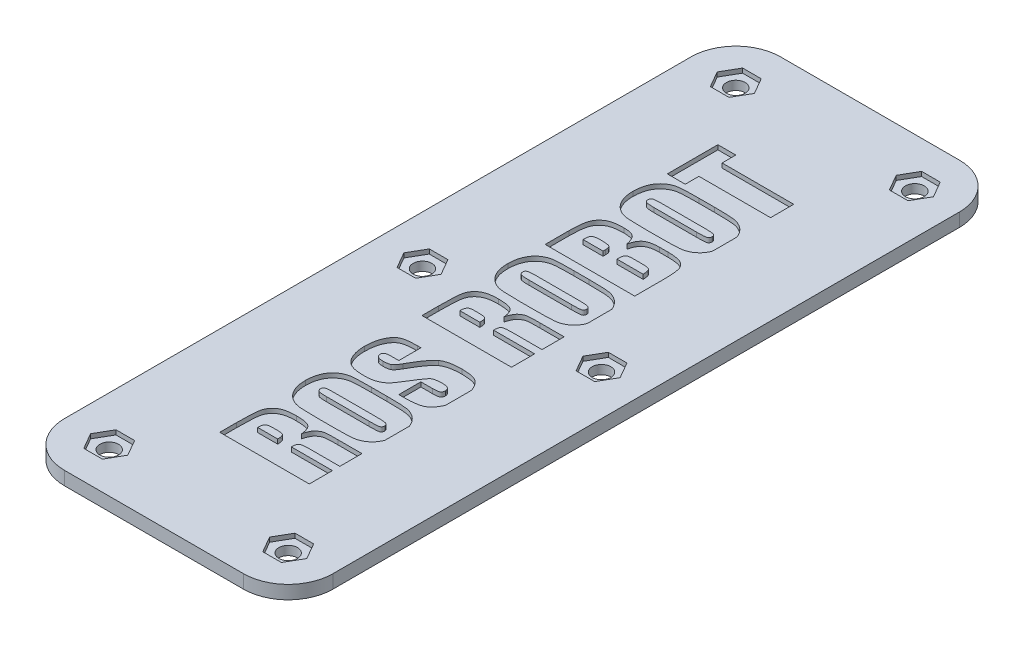
SolidWorks part; units mm, degrees
ref_plane "Front Plane" through (0, 0, 0) normal (0, 0, 1) x (1, 0, 0)
ref_plane "Top Plane" through (0, 0, 0) normal (0, 1, 0) x (1, 0, 0)
ref_plane "Right Plane" through (0, 0, 0) normal (1, 0, 0) x (0, 0, -1)
sketch "Sketch1" plane through (0, 0, 0) normal (0, 1, 0) x (1, 0, 0)
  line L1 (-30, 80) -> (30, 80)
  line L2 (-30, 80) -> (-30, -80)
  line L3 (-30, -80) -> (30, -80)
  line L4 (30, 80) -> (30, -80)
  line L5 (-30, 80) -> (30, -80) construction
  line L6 (-30, -80) -> (30, 80) construction
  point P0 (0, 0)
  dimension "D1" = 60
  dimension "D2" = 160
extrude "Boss-Extrude1" add sketch "Sketch1" along normal blind 3
sketch "Sketch2" plane through (0, 3, 0) normal (0, 1, 0) x (1, 0, 0)
  line L0 (-30, -80) -> (30, -80) construction
  line L2 (-30, 80) -> (-30, -80) construction
  circle A0 centre (-20, -70) radius 2.09
  circle A1 centre (-20, 0) radius 2.09
  circle A2 centre (-20, 70) radius 2.09
  dimension "D1" = 4.18
  dimension "D2" = 70
  dimension "D3" = 70
  dimension "D4" = 10
  dimension "D5" = 10
extrude "Cut-Extrude1" cut sketch "Sketch2" against normal through all
mirror "Mirror1" about plane through (0, 0, 0) normal (1, 0, 0) of "Cut-Extrude1"
sketch "Sketch3" plane through (0, 3, 0) normal (0, 1, 0) x (1, 0, 0)
  line L0 (10, -60) -> (10, 60)
  line L1 (-30, 80) -> (-30, -80) construction
  line L2 (-10, -55.2941) -> (-10, -51.5662)
  line L3 (4.6581, -43.5294) -> (10, -43.5294)
  line L4 (10, -43.5294) -> (10, -48.4706)
  line L5 (10, -48.4706) -> (3.2353, -48.4706)
  line L6 (0.8235, -50.1176) -> (10, -50.1176)
  line L7 (10, -50.1176) -> (10, -55.2941)
  line L8 (10, -55.2941) -> (-10, -55.2941)
  line L9 (-6.7059, -50.1176) -> (-2.2353, -50.1176)
  line L10 (-4.0478, -48.4706) -> (-5.1544, -48.4706)
  line L11 (1.7206, -41.6471) -> (-1.7206, -41.6471)
  line L12 (-1.7206, -29.6471) -> (1.7206, -29.6471)
  line L13 (-4.9596, -36.4706) -> (4.5662, -36.4706)
  line L14 (4.4154, -34.8235) -> (-4.9596, -34.8235)
  line L15 (-3.8824, -16.4706) -> (-3.8824, -21.4118)
  line L16 (-3.8824, -21.4118) -> (-5.4632, -21.4118)
  line L17 (4.0478, -28) -> (2.7059, -28)
  line L18 (2.7059, -28) -> (2.7059, -23.0588)
  line L19 (2.7059, -23.0588) -> (5.2978, -23.0588)
  line L20 (-4.6875, -16.4706) -> (-3.8824, -16.4706)
  line L21 (-10, -10.1176) -> (-10, -6.3897)
  line L22 (4.6581, 1.6471) -> (10, 1.6471)
  line L23 (10, 1.6471) -> (10, -3.2941)
  line L24 (10, -3.2941) -> (3.2353, -3.2941)
  line L25 (0.8235, -4.9412) -> (10, -4.9412)
  line L26 (10, -4.9412) -> (10, -10.1176)
  line L27 (10, -10.1176) -> (-10, -10.1176)
  line L28 (-6.7059, -4.9412) -> (-2.2353, -4.9412)
  line L29 (-4.0478, -3.2941) -> (-5.1544, -3.2941)
  line L30 (1.7206, 3.5294) -> (-1.7206, 3.5294)
  line L31 (-1.7206, 15.5294) -> (1.7206, 15.5294)
  line L32 (-4.9596, 8.7059) -> (4.5662, 8.7059)
  line L33 (4.4154, 10.3529) -> (-4.9596, 10.3529)
  line L34 (-10, 17.4118) -> (-10, 22.7169)
  line L35 (3.364, 29.6471) -> (5.2426, 29.6471)
  line L36 (10, 23.4926) -> (10, 17.4118)
  line L37 (10, 17.4118) -> (-10, 17.4118)
  line L38 (-6.7059, 22.5882) -> (-2.2353, 22.5882)
  line L39 (0.8235, 22.5882) -> (6.7059, 22.5882)
  line L40 (4.7463, 24.4706) -> (2.7831, 24.4706)
  line L41 (1.7206, 31.5294) -> (-1.7206, 31.5294)
  line L42 (-1.7206, 43.5294) -> (1.7206, 43.5294)
  line L43 (-4.9596, 36.7059) -> (4.5662, 36.7059)
  line L44 (4.4154, 38.3529) -> (-4.9596, 38.3529)
  line L45 (-10, 56) -> (-6, 56)
  line L46 (-6, 56) -> (-6, 52.9412)
  line L47 (-6, 52.9412) -> (10, 52.9412)
  line L48 (10, 52.9412) -> (10, 47.7647)
  line L49 (10, 47.7647) -> (-6, 47.7647)
  line L50 (-6, 47.7647) -> (-6, 44.7059)
  line L51 (-6, 44.7059) -> (-10, 44.7059)
  line L52 (-10, 44.7059) -> (-10, 56)
  spline S0 degree 3 poles (-10, -51.5662) (-10.0021, -50.9938) (-9.9925, -50.1738) (-9.9618, -49.131) (-9.9343, -48.4616) (-9.8938, -47.8671) (-9.8469, -47.3485) (-9.7938, -46.9053) (-9.7279, -46.5265) (-9.6422, -46.1927) (-9.5296, -45.8846) (-9.3956, -45.5898) (-9.2282, -45.3117) (-9.0316, -45.0523) (-8.8156, -44.8023) (-8.5646, -44.5748) (-8.2904, -44.3559) (-7.9777, -44.158) (-7.6226, -43.9907) (-7.2263, -43.847) (-6.7869, -43.7305) (-6.3051, -43.6403) (-5.579, -43.5478) (-5.0099, -43.5348) (-4.6176, -43.5294) knots 0 0 0 0 0.148881 0.213303 0.271377 0.323138 0.368276 0.406827 0.439217 0.468212 0.496346 0.524443 0.552325 0.580569 0.609028 0.638128 0.668547 0.700209 0.734143 0.770448 0.80973 0.852244 0.897872 1 1 1 1
  spline S1 degree 3 poles (-4.6176, -43.5294) (-4.2653, -43.5236) (-3.7599, -43.5474) (-3.1182, -43.6025) (-2.7075, -43.671) (-2.3432, -43.7491) (-2.0238, -43.8459) (-1.7543, -43.9676) (-1.5246, -44.1057) (-1.3304, -44.2743) (-1.1605, -44.4757) (-1.0104, -44.7121) (-0.8806, -44.9835) (-0.7776, -45.291) (-0.6464, -45.7633) (-0.5975, -46.1443) (-0.5735, -46.4081) knots 0 0 0 0 0.183844 0.264214 0.336185 0.401092 0.458783 0.510057 0.555172 0.598283 0.643683 0.692329 0.744143 0.800414 0.861431 1 1 1 1
  spline S2 degree 3 poles (-0.5735, -46.4081) (-0.5082, -46.1692) (-0.4158, -45.8227) (-0.2536, -45.3924) (-0.1242, -45.1174) (0.0082, -44.8722) (0.1462, -44.6567) (0.2982, -44.4752) (0.5056, -44.2791) (0.7695, -44.0853) (1.0739, -43.8901) (1.3668, -43.7472) (1.6163, -43.6653) (1.8438, -43.6284) (2.0703, -43.5981) (2.3577, -43.579) (2.7033, -43.5604) (3.1078, -43.5466) (3.7658, -43.5296) (4.2893, -43.5348) (4.6581, -43.5294) knots 0 0 0 0 0.11021 0.159198 0.204304 0.245276 0.283065 0.317885 0.350264 0.409778 0.463156 0.510931 0.554366 0.579275 0.613344 0.655979 0.70728 0.767268 0.835956 1 1 1 1
  spline S3 degree 3 poles (3.2353, -48.4706) (2.989, -48.4726) (2.6391, -48.4726) (2.1993, -48.5048) (1.9269, -48.5332) (1.6924, -48.5693) (1.4957, -48.6105) (1.339, -48.6657) (1.2146, -48.7289) (1.114, -48.8112) (1.0393, -48.9233) (0.9667, -49.0542) (0.9194, -49.2179) (0.8733, -49.4037) (0.8356, -49.7073) (0.824, -49.9481) (0.8235, -50.1176) knots 0 0 0 0 0.208735 0.296167 0.373443 0.440695 0.497113 0.543415 0.581035 0.614932 0.652106 0.694368 0.741317 0.795712 0.856499 1 1 1 1
  spline S4 degree 3 poles (-2.2353, -50.1176) (-2.241, -49.859) (-2.2449, -49.4942) (-2.3595, -49.0703) (-2.4455, -48.8674) (-2.5571, -48.7457) (-2.6702, -48.6674) (-2.8204, -48.6082) (-3.0015, -48.5571) (-3.2158, -48.5182) (-3.5672, -48.4758) (-3.8494, -48.4762) (-4.0478, -48.4706) knots 0 0 0 0 0.26299 0.361623 0.442867 0.481356 0.526611 0.580322 0.643299 0.716254 0.799641 1 1 1 1
  spline S5 degree 3 poles (-5.1544, -48.4706) (-5.4183, -48.4732) (-5.7882, -48.4915) (-6.209, -48.649) (-6.422, -48.8134) (-6.5523, -49.0502) (-6.6913, -49.4796) (-6.7008, -49.8538) (-6.7059, -50.1176) knots 0 0 0 0 0.296724 0.405999 0.497474 0.590179 0.702697 1 1 1 1
  spline S6 degree 3 poles (1.7206, -29.6471) (2.1887, -29.6516) (2.8628, -29.6489) (3.7244, -29.6629) (4.2868, -29.6838) (4.7956, -29.6992) (5.249, -29.7256) (5.6474, -29.7548) (6.1016, -29.7961) (6.625, -29.8819) (7.2194, -30.0688) (7.7848, -30.3319) (8.3184, -30.6676) (8.8126, -31.0692) (9.2459, -31.5466) (9.6203, -32.0876) (9.9272, -32.6949) (10.1748, -33.3563) (10.4086, -34.3407) (10.4749, -35.116) (10.4706, -35.6471) knots 0 0 0 0 0.113101 0.162848 0.208171 0.249056 0.285827 0.31789 0.345554 0.396029 0.44566 0.495598 0.546282 0.597611 0.648955 0.701516 0.75607 0.812935 0.871747 1 1 1 1
  spline S7 degree 3 poles (10.4706, -35.6471) (10.4702, -36.1567) (10.4117, -36.9073) (10.1869, -37.8648) (9.9551, -38.5228) (9.666, -39.1346) (9.2939, -39.6787) (8.8684, -40.1717) (8.3693, -40.5862) (7.8326, -40.9353) (7.2648, -41.2061) (6.6744, -41.4) (6.1562, -41.4954) (5.705, -41.5355) (5.3079, -41.5652) (4.8519, -41.59) (4.3384, -41.6129) (3.766, -41.6259) (2.8873, -41.6415) (2.1985, -41.6458) (1.7206, -41.6471) knots 0 0 0 0 0.123187 0.181008 0.237203 0.291505 0.343988 0.396026 0.44835 0.500181 0.550382 0.599921 0.649928 0.677302 0.709372 0.746151 0.787647 0.833563 0.884505 1 1 1 1
  spline S8 degree 3 poles (-1.7206, -41.6471) (-2.1875, -41.6426) (-2.8616, -41.6453) (-3.7232, -41.6312) (-4.2868, -41.6107) (-4.7942, -41.5935) (-5.2479, -41.5731) (-5.6461, -41.5428) (-6.102, -41.5024) (-6.6245, -41.4108) (-7.2196, -41.2259) (-7.7852, -40.961) (-8.3211, -40.6288) (-8.8141, -40.2235) (-9.2437, -39.7445) (-9.6213, -39.2061) (-9.9283, -38.5999) (-10.1693, -37.9353) (-10.4131, -36.9536) (-10.4652, -36.1757) (-10.4706, -35.6471) knots 0 0 0 0 0.112808 0.162853 0.208178 0.249064 0.285525 0.317884 0.345549 0.396077 0.445709 0.495649 0.546586 0.597688 0.649252 0.701572 0.756128 0.812892 0.872063 1 1 1 1
  spline S9 degree 3 poles (-10.4706, -35.6471) (-10.4714, -35.1372) (-10.4096, -34.3888) (-10.1907, -33.4315) (-9.9597, -32.7739) (-9.664, -32.1639) (-9.2966, -31.6157) (-8.8667, -31.1263) (-8.3697, -30.7111) (-7.8316, -30.3634) (-7.2658, -30.087) (-6.6754, -29.8952) (-6.1588, -29.7978) (-5.7072, -29.7597) (-5.3094, -29.7227) (-4.8517, -29.7062) (-4.3385, -29.6803) (-3.7659, -29.6698) (-2.8875, -29.6434) (-2.1984, -29.6546) (-1.7206, -29.6471) knots 0 0 0 0 0.123194 0.180663 0.236861 0.291296 0.344027 0.395847 0.448174 0.500008 0.55034 0.599882 0.649601 0.676977 0.709367 0.746132 0.787631 0.833549 0.884501 1 1 1 1
  spline S10 degree 3 poles (-4.9596, -34.8235) (-5.1753, -34.8242) (-5.4829, -34.83) (-5.8716, -34.843) (-6.1155, -34.8622) (-6.3276, -34.8839) (-6.5086, -34.9074) (-6.6559, -34.9406) (-6.806, -34.9862) (-6.954, -35.0702) (-7.1431, -35.2687) (-7.1725, -35.486) (-7.1765, -35.6213) knots 0 0 0 0 0.245382 0.350014 0.44228 0.523563 0.592561 0.649714 0.69512 0.770679 0.840726 1 1 1 1
  spline S11 degree 3 poles (-7.1765, -35.6213) (-7.1826, -35.7474) (-7.1389, -35.933) (-7.0007, -36.1393) (-6.8803, -36.2454) (-6.7481, -36.3134) (-6.606, -36.3546) (-6.4264, -36.3903) (-6.2075, -36.4176) (-5.9516, -36.4453) (-5.5307, -36.4612) (-5.1963, -36.473) (-4.9596, -36.4706) knots 0 0 0 0 0.14123 0.20787 0.277368 0.319365 0.374393 0.44345 0.525667 0.62281 0.733417 1 1 1 1
  spline S12 degree 3 poles (4.5662, -36.4706) (4.8346, -36.4661) (5.2158, -36.4689) (5.6951, -36.4552) (5.9902, -36.4341) (6.2432, -36.4194) (6.4541, -36.3928) (6.6225, -36.365) (6.7864, -36.3252) (6.9456, -36.2427) (7.1431, -36.032) (7.1757, -35.8027) (7.1765, -35.6581) knots 0 0 0 0 0.263966 0.37491 0.47152 0.554902 0.624119 0.680394 0.722784 0.789642 0.853612 1 1 1 1
  spline S13 degree 3 poles (7.1765, -35.6581) (7.1748, -35.5096) (7.1356, -35.267) (6.9074, -35.0588) (6.7277, -34.9785) (6.5458, -34.9318) (6.3632, -34.9057) (6.1401, -34.8796) (5.8753, -34.8573) (5.5687, -34.8447) (5.0773, -34.8286) (4.6887, -34.825) (4.4154, -34.8235) knots 0 0 0 0 0.144509 0.209626 0.282207 0.327425 0.385695 0.455209 0.538352 0.635125 0.743353 1 1 1 1
  spline S14 degree 3 poles (-5.4632, -21.4118) (-5.765, -21.4118) (-6.1723, -21.4209) (-6.6458, -21.5046) (-6.8672, -21.593) (-7.0158, -21.7183) (-7.1437, -21.9403) (-7.1819, -22.1356) (-7.1765, -22.2721) knots 0 0 0 0 0.412531 0.554325 0.654756 0.734266 0.814634 1 1 1 1
  spline S15 degree 3 poles (-7.1765, -22.2721) (-7.1753, -22.4224) (-7.1339, -22.6526) (-6.9564, -22.8986) (-6.7779, -23.0494) (-6.5473, -23.1638) (-6.1427, -23.267) (-5.8109, -23.3007) (-5.5735, -23.2941) knots 0 0 0 0 0.212113 0.312859 0.418563 0.535756 0.66915 1 1 1 1
  spline S16 degree 3 poles (-5.5735, -23.2941) (-5.2685, -23.2963) (-4.7355, -23.2666) (-4.2139, -23.1434) (-4.0074, -23.0441) knots 0 0 0 0 0.572651 1 1 1 1
  spline S17 degree 3 poles (-4.0074, -23.0441) (-3.9087, -22.9953) (-3.7635, -22.892) (-3.5783, -22.7165) (-3.4317, -22.5391) (-3.2741, -22.3344) (-3.0492, -21.9996) (-2.8928, -21.7223) (-2.7831, -21.5294) knots 0 0 0 0 0.166753 0.269572 0.387216 0.516182 0.662459 1 1 1 1
  spline S18 degree 3 poles (-2.7831, -21.5294) (-2.4734, -20.9703) (-2.0184, -20.1729) (-1.3881, -19.1897) (-0.9563, -18.5738) (-0.5522, -18.0389) (-0.0677, -17.4805) (0.3024, -17.1194) (0.5662, -16.9375) knots 0 0 0 0 0.335278 0.4813 0.612364 0.729739 0.832713 1 1 1 1
  spline S19 degree 3 poles (0.5662, -16.9375) (0.806, -16.77) (1.2115, -16.5589) (1.8106, -16.3573) (2.3243, -16.226) (2.8906, -16.1237) (3.7446, -16.0244) (4.4137, -16) (4.875, -16) knots 0 0 0 0 0.195997 0.304678 0.423526 0.551406 0.690506 1 1 1 1
  spline S20 degree 3 poles (4.875, -16) (5.2122, -15.9983) (5.6998, -16.0135) (6.3256, -16.0701) (6.7422, -16.1221) (7.1236, -16.1969) (7.469, -16.2838) (7.7801, -16.385) (8.0583, -16.5087) (8.3139, -16.656) (8.557, -16.8277) (8.7858, -17.0338) (9.0067, -17.2654) (9.2179, -17.528) (9.4131, -17.8237) (9.6079, -18.1433) (9.8414, -18.6198) (10.1006, -19.2594) (10.3969, -20.3943) (10.4676, -21.2925) (10.4706, -21.9044) knots 0 0 0 0 0.107325 0.155097 0.199939 0.240858 0.278693 0.313224 0.344823 0.375395 0.406993 0.439316 0.473245 0.508753 0.546395 0.585923 0.627781 0.715119 0.805079 1 1 1 1
  spline S21 degree 3 poles (10.4706, -21.9044) (10.4757, -22.2484) (10.4446, -22.7548) (10.3628, -23.4141) (10.2732, -23.8804) (10.1612, -24.328) (10.0192, -24.7555) (9.8605, -25.1658) (9.6676, -25.5494) (9.4591, -25.9093) (9.2368, -26.2396) (8.9991, -26.5368) (8.7496, -26.8027) (8.4841, -27.0361) (8.2022, -27.235) (7.9096, -27.4062) (7.5968, -27.5388) (7.2633, -27.6501) (6.9011, -27.7452) (6.505, -27.82) (6.0773, -27.8875) (5.616, -27.9373) (4.936, -27.9878) (4.4094, -27.9998) (4.0478, -28) knots 0 0 0 0 0.100148 0.147671 0.19347 0.238417 0.282003 0.324638 0.366476 0.406958 0.44578 0.482362 0.517724 0.551885 0.585175 0.618127 0.650431 0.683967 0.720516 0.759451 0.801367 0.846634 0.894615 1 1 1 1
  spline S22 degree 3 poles (5.2978, -23.0588) (5.4794, -23.0613) (5.7378, -23.049) (6.0657, -23.0335) (6.2711, -23.0047) (6.4517, -22.98) (6.6031, -22.9371) (6.7301, -22.8953) (6.8628, -22.8277) (6.9937, -22.7117) (7.1506, -22.4544) (7.1729, -22.2151) (7.1765, -22.0551) knots 0 0 0 0 0.221449 0.31586 0.400263 0.474516 0.538003 0.591926 0.637412 0.719013 0.801608 1 1 1 1
  spline S23 degree 3 poles (7.1765, -22.0551) (7.1797, -21.8865) (7.1319, -21.6346) (6.944, -21.3618) (6.7516, -21.2047) (6.511, -21.0827) (6.094, -20.9668) (5.75, -20.942) (5.5074, -20.9412) knots 0 0 0 0 0.223439 0.325747 0.431377 0.547858 0.679404 1 1 1 1
  spline S24 degree 3 poles (5.5074, -20.9412) (5.2301, -20.9407) (4.8335, -20.9536) (4.3315, -21.0008) (4.0144, -21.0585) (3.7334, -21.12) (3.4321, -21.228) (3.2311, -21.3302) (3.125, -21.4228) knots 0 0 0 0 0.33668 0.481833 0.611779 0.728037 0.830669 1 1 1 1
  spline S25 degree 3 poles (3.125, -21.4228) (3.0067, -21.5278) (2.832, -21.7237) (2.5986, -22.0274) (2.3862, -22.3232) (2.1458, -22.6637) (1.7857, -23.219) (1.5142, -23.6656) (1.3235, -23.9779) knots 0 0 0 0 0.151179 0.250673 0.366592 0.499698 0.649697 1 1 1 1
  spline S26 degree 3 poles (1.3235, -23.9779) (1.1312, -24.2944) (0.8539, -24.7471) (0.4867, -25.3154) (0.2465, -25.6779) (0.024, -25.9952) (-0.1732, -26.2708) (-0.3489, -26.5042) (-0.5602, -26.7562) (-0.8385, -27.0321) (-1.2198, -27.322) (-1.6571, -27.5826) (-2.1499, -27.8167) (-2.7079, -28.0109) (-3.5918, -28.187) (-4.2954, -28.2419) (-4.7868, -28.2353) knots 0 0 0 0 0.139506 0.199942 0.254867 0.303273 0.345934 0.382495 0.413289 0.469759 0.52968 0.593251 0.661185 0.734906 0.815121 1 1 1 1
  spline S27 degree 3 poles (-4.7868, -28.2353) (-5.1483, -28.2299) (-5.6721, -28.2229) (-6.342, -28.1555) (-6.7866, -28.0911) (-7.1929, -28.0062) (-7.5618, -27.9063) (-7.8893, -27.7803) (-8.183, -27.6392) (-8.4486, -27.4744) (-8.6932, -27.2854) (-8.9296, -27.0793) (-9.1431, -26.8428) (-9.3479, -26.5869) (-9.5388, -26.3089) (-9.711, -26.0053) (-9.9259, -25.5665) (-10.1466, -24.9651) (-10.4114, -23.8851) (-10.4702, -23.0241) (-10.4706, -22.4338) knots 0 0 0 0 0.115094 0.16642 0.214115 0.25793 0.298418 0.335563 0.369391 0.401957 0.434786 0.46765 0.501588 0.535991 0.571894 0.608743 0.64693 0.727243 0.81197 1 1 1 1
  spline S28 degree 3 poles (-10.4706, -22.4338) (-10.4681, -22.0991) (-10.4534, -21.6059) (-10.3832, -20.9641) (-10.3105, -20.511) (-10.2136, -20.0772) (-10.102, -19.6612) (-9.9641, -19.2668) (-9.8111, -18.8916) (-9.6395, -18.5421) (-9.457, -18.2203) (-9.2585, -17.9336) (-9.0613, -17.6686) (-8.8392, -17.446) (-8.617, -17.2428) (-8.377, -17.0786) (-8.1223, -16.9405) (-7.8384, -16.8309) (-7.5198, -16.7307) (-7.1549, -16.6529) (-6.7482, -16.5815) (-6.2949, -16.5328) (-5.6039, -16.4819) (-5.0626, -16.471) (-4.6875, -16.4706) knots 0 0 0 0 0.103075 0.151642 0.198646 0.244222 0.288419 0.331123 0.37273 0.413047 0.450895 0.486465 0.520341 0.552351 0.583079 0.612899 0.641587 0.672056 0.706415 0.744299 0.786776 0.83347 0.88453 1 1 1 1
  spline S29 degree 3 poles (-10, -6.3897) (-10.0021, -5.8173) (-9.9925, -4.9973) (-9.9618, -3.9545) (-9.9343, -3.2851) (-9.8938, -2.6907) (-9.8469, -2.172) (-9.7938, -1.7288) (-9.7279, -1.3501) (-9.6422, -1.0162) (-9.5296, -0.7081) (-9.3956, -0.4133) (-9.2282, -0.1353) (-9.0316, 0.1241) (-8.8156, 0.3741) (-8.5646, 0.6016) (-8.2904, 0.8205) (-7.9777, 1.0184) (-7.6226, 1.1858) (-7.2263, 1.3294) (-6.7869, 1.4459) (-6.3051, 1.5362) (-5.579, 1.6287) (-5.0099, 1.6416) (-4.6176, 1.6471) knots 0 0 0 0 0.148881 0.213303 0.271377 0.323138 0.368276 0.406827 0.439217 0.468212 0.496346 0.524443 0.552325 0.580569 0.609028 0.638128 0.668547 0.700209 0.734143 0.770448 0.80973 0.852244 0.897872 1 1 1 1
  spline S30 degree 3 poles (-4.6176, 1.6471) (-4.2653, 1.6529) (-3.7599, 1.629) (-3.1182, 1.574) (-2.7075, 1.5055) (-2.3432, 1.4273) (-2.0238, 1.3305) (-1.7543, 1.2089) (-1.5246, 1.0707) (-1.3304, 0.9022) (-1.1605, 0.7008) (-1.0104, 0.4644) (-0.8806, 0.1929) (-0.7776, -0.1145) (-0.6464, -0.5869) (-0.5975, -0.9678) (-0.5735, -1.2316) knots 0 0 0 0 0.183844 0.264214 0.336185 0.401092 0.458783 0.510057 0.555172 0.598283 0.643683 0.692329 0.744143 0.800414 0.861431 1 1 1 1
  spline S31 degree 3 poles (-0.5735, -1.2316) (-0.5082, -0.9927) (-0.4158, -0.6463) (-0.2536, -0.216) (-0.1242, 0.0591) (0.0082, 0.3043) (0.1462, 0.5197) (0.2982, 0.7013) (0.5056, 0.8974) (0.7695, 1.0911) (1.0739, 1.2863) (1.3668, 1.4293) (1.6163, 1.5112) (1.8438, 1.5481) (2.0703, 1.5783) (2.3577, 1.5974) (2.7033, 1.6161) (3.1078, 1.6299) (3.7658, 1.6469) (4.2893, 1.6416) (4.6581, 1.6471) knots 0 0 0 0 0.11021 0.159198 0.204304 0.245276 0.283065 0.317885 0.350264 0.409778 0.463156 0.510931 0.554366 0.579275 0.613344 0.655979 0.70728 0.767268 0.835956 1 1 1 1
  spline S32 degree 3 poles (3.2353, -3.2941) (2.989, -3.2962) (2.6391, -3.2961) (2.1993, -3.3283) (1.9269, -3.3567) (1.6924, -3.3928) (1.4957, -3.4341) (1.339, -3.4893) (1.2146, -3.5525) (1.114, -3.6348) (1.0393, -3.7469) (0.9667, -3.8778) (0.9194, -4.0414) (0.8733, -4.2272) (0.8356, -4.5308) (0.824, -4.7717) (0.8235, -4.9412) knots 0 0 0 0 0.208735 0.296167 0.373443 0.440695 0.497113 0.543415 0.581035 0.614932 0.652106 0.694368 0.741317 0.795712 0.856499 1 1 1 1
  spline S33 degree 3 poles (-2.2353, -4.9412) (-2.241, -4.6826) (-2.2449, -4.3177) (-2.3595, -3.8938) (-2.4455, -3.6909) (-2.5571, -3.5692) (-2.6702, -3.491) (-2.8204, -3.4317) (-3.0015, -3.3807) (-3.2158, -3.3417) (-3.5672, -3.2993) (-3.8494, -3.2997) (-4.0478, -3.2941) knots 0 0 0 0 0.26299 0.361623 0.442867 0.481356 0.526611 0.580322 0.643299 0.716254 0.799641 1 1 1 1
  spline S34 degree 3 poles (-5.1544, -3.2941) (-5.4183, -3.2968) (-5.7882, -3.315) (-6.209, -3.4725) (-6.422, -3.6369) (-6.5523, -3.8737) (-6.6913, -4.3032) (-6.7008, -4.6773) (-6.7059, -4.9412) knots 0 0 0 0 0.296724 0.405999 0.497474 0.590179 0.702697 1 1 1 1
  spline S35 degree 3 poles (1.7206, 15.5294) (2.1887, 15.5249) (2.8628, 15.5276) (3.7244, 15.5136) (4.2868, 15.4926) (4.7956, 15.4773) (5.249, 15.4509) (5.6474, 15.4217) (6.1016, 15.3804) (6.625, 15.2946) (7.2194, 15.1077) (7.7848, 14.8446) (8.3184, 14.5089) (8.8126, 14.1073) (9.2459, 13.6298) (9.6203, 13.0889) (9.9272, 12.4816) (10.1748, 11.8202) (10.4086, 10.8357) (10.4749, 10.0605) (10.4706, 9.5294) knots 0 0 0 0 0.113101 0.162848 0.208171 0.249056 0.285827 0.31789 0.345554 0.396029 0.44566 0.495598 0.546282 0.597611 0.648955 0.701516 0.75607 0.812935 0.871747 1 1 1 1
  spline S36 degree 3 poles (10.4706, 9.5294) (10.4702, 9.0198) (10.4117, 8.2692) (10.1869, 7.3116) (9.9551, 6.6537) (9.666, 6.0419) (9.2939, 5.4977) (8.8684, 5.0048) (8.3693, 4.5903) (7.8326, 4.2412) (7.2648, 3.9704) (6.6744, 3.7764) (6.1562, 3.681) (5.705, 3.6409) (5.3079, 3.6113) (4.8519, 3.5865) (4.3384, 3.5636) (3.766, 3.5505) (2.8873, 3.535) (2.1985, 3.5307) (1.7206, 3.5294) knots 0 0 0 0 0.123187 0.181008 0.237203 0.291505 0.343988 0.396026 0.44835 0.500181 0.550382 0.599921 0.649928 0.677302 0.709372 0.746151 0.787647 0.833563 0.884505 1 1 1 1
  spline S37 degree 3 poles (-1.7206, 3.5294) (-2.1875, 3.5339) (-2.8616, 3.5312) (-3.7232, 3.5453) (-4.2868, 3.5657) (-4.7942, 3.5829) (-5.2479, 3.6034) (-5.6461, 3.6337) (-6.102, 3.674) (-6.6245, 3.7656) (-7.2196, 3.9505) (-7.7852, 4.2155) (-8.3211, 4.5477) (-8.8141, 4.953) (-9.2437, 5.432) (-9.6213, 5.9703) (-9.9283, 6.5765) (-10.1693, 7.2411) (-10.4131, 8.2229) (-10.4652, 9.0008) (-10.4706, 9.5294) knots 0 0 0 0 0.112808 0.162853 0.208178 0.249064 0.285525 0.317884 0.345549 0.396077 0.445709 0.495649 0.546586 0.597688 0.649252 0.701572 0.756128 0.812892 0.872063 1 1 1 1
  spline S38 degree 3 poles (-10.4706, 9.5294) (-10.4714, 10.0393) (-10.4096, 10.7877) (-10.1907, 11.7449) (-9.9597, 12.4026) (-9.664, 13.0126) (-9.2966, 13.5607) (-8.8667, 14.0501) (-8.3697, 14.4654) (-7.8316, 14.813) (-7.2658, 15.0895) (-6.6754, 15.2813) (-6.1588, 15.3787) (-5.7072, 15.4167) (-5.3094, 15.4538) (-4.8517, 15.4703) (-4.3385, 15.4962) (-3.7659, 15.5067) (-2.8875, 15.5331) (-2.1984, 15.5218) (-1.7206, 15.5294) knots 0 0 0 0 0.123194 0.180663 0.236861 0.291296 0.344027 0.395847 0.448174 0.500008 0.55034 0.599882 0.649601 0.676977 0.709367 0.746132 0.787631 0.833549 0.884501 1 1 1 1
  spline S39 degree 3 poles (-4.9596, 10.3529) (-5.1753, 10.3523) (-5.4829, 10.3464) (-5.8716, 10.3334) (-6.1155, 10.3143) (-6.3276, 10.2926) (-6.5086, 10.2691) (-6.6559, 10.2359) (-6.806, 10.1902) (-6.954, 10.1063) (-7.1431, 9.9078) (-7.1725, 9.6905) (-7.1765, 9.5551) knots 0 0 0 0 0.245382 0.350014 0.44228 0.523563 0.592561 0.649714 0.69512 0.770679 0.840726 1 1 1 1
  spline S40 degree 3 poles (-7.1765, 9.5551) (-7.1826, 9.4291) (-7.1389, 9.2435) (-7.0007, 9.0372) (-6.8803, 8.931) (-6.7481, 8.8631) (-6.606, 8.8219) (-6.4264, 8.7862) (-6.2075, 8.7588) (-5.9516, 8.7312) (-5.5307, 8.7153) (-5.1963, 8.7035) (-4.9596, 8.7059) knots 0 0 0 0 0.14123 0.20787 0.277368 0.319365 0.374393 0.44345 0.525667 0.62281 0.733417 1 1 1 1
  spline S41 degree 3 poles (4.5662, 8.7059) (4.8346, 8.7104) (5.2158, 8.7076) (5.6951, 8.7213) (5.9902, 8.7424) (6.2432, 8.7571) (6.4541, 8.7836) (6.6225, 8.8115) (6.7864, 8.8513) (6.9456, 8.9338) (7.1431, 9.1444) (7.1757, 9.3737) (7.1765, 9.5184) knots 0 0 0 0 0.263966 0.37491 0.47152 0.554902 0.624119 0.680394 0.722784 0.789642 0.853612 1 1 1 1
  spline S42 degree 3 poles (7.1765, 9.5184) (7.1748, 9.6669) (7.1356, 9.9095) (6.9074, 10.1176) (6.7277, 10.198) (6.5458, 10.2447) (6.3632, 10.2708) (6.1401, 10.2969) (5.8753, 10.3191) (5.5687, 10.3318) (5.0773, 10.3479) (4.6887, 10.3515) (4.4154, 10.3529) knots 0 0 0 0 0.144509 0.209626 0.282207 0.327425 0.385695 0.455209 0.538352 0.635125 0.743353 1 1 1 1
  spline S43 degree 3 poles (-10, 22.7169) (-9.9955, 23.1103) (-9.9921, 23.6819) (-9.9527, 24.4186) (-9.9071, 24.9135) (-9.857, 25.3711) (-9.7961, 25.7911) (-9.7188, 26.1725) (-9.6309, 26.5207) (-9.5237, 26.8424) (-9.3912, 27.1434) (-9.2355, 27.4283) (-9.0587, 27.6987) (-8.8552, 27.9531) (-8.6276, 28.1917) (-8.375, 28.4137) (-8.0977, 28.6217) (-7.7862, 28.8126) (-7.4301, 28.9734) (-7.0293, 29.1081) (-6.5873, 29.2218) (-6.1, 29.3043) (-5.3665, 29.3894) (-4.791, 29.4161) (-4.3934, 29.4118) knots 0 0 0 0 0.114375 0.166108 0.21439 0.258844 0.299904 0.337701 0.371916 0.404248 0.43615 0.467396 0.498519 0.529953 0.561953 0.594259 0.627603 0.66261 0.70023 0.740899 0.785396 0.832777 0.884431 1 1 1 1
  spline S44 degree 3 poles (-4.3934, 29.4118) (-4.127, 29.416) (-3.7431, 29.3962) (-3.2561, 29.335) (-2.9376, 29.2799) (-2.6536, 29.1963) (-2.3989, 29.1046) (-2.1784, 28.9884) (-1.985, 28.8544) (-1.8163, 28.6891) (-1.6558, 28.4982) (-1.5162, 28.2669) (-1.3783, 28.0074) (-1.2489, 27.7134) (-1.0963, 27.2527) (-0.9938, 26.8887) (-0.9412, 26.6324) knots 0 0 0 0 0.159635 0.229972 0.294227 0.35305 0.407212 0.456169 0.502024 0.547743 0.597307 0.65111 0.709269 0.77341 0.843331 1 1 1 1
  spline S45 degree 3 poles (-0.9412, 26.6324) (-0.8783, 26.9064) (-0.7658, 27.3007) (-0.5629, 27.7876) (-0.4027, 28.1069) (-0.2205, 28.3873) (-0.0268, 28.6367) (0.1878, 28.8487) (0.4252, 29.025) (0.6872, 29.1721) (0.9755, 29.3025) (1.2968, 29.4066) (1.6481, 29.495) (2.0311, 29.565) (2.6061, 29.6282) (3.0548, 29.6461) (3.364, 29.6471) knots 0 0 0 0 0.144043 0.209309 0.269932 0.32668 0.380292 0.431325 0.480651 0.531247 0.584899 0.64245 0.703941 0.770287 0.841669 1 1 1 1
  spline S46 degree 3 poles (5.2426, 29.6471) (5.5626, 29.6468) (6.0268, 29.6352) (6.6234, 29.5846) (7.0212, 29.535) (7.3857, 29.4682) (7.7163, 29.3886) (8.0154, 29.2938) (8.3632, 29.1496) (8.7467, 28.9274) (9.131, 28.5817) (9.4335, 28.1642) (9.6212, 27.7575) (9.7292, 27.3755) (9.8021, 27.0179) (9.8619, 26.5942) (9.9131, 26.1025) (9.9518, 25.5458) (9.9944, 24.6684) (9.9944, 23.9766) (10, 23.4926) knots 0 0 0 0 0.102269 0.148253 0.191288 0.230306 0.266588 0.299901 0.330446 0.386794 0.440584 0.494395 0.550463 0.582684 0.621084 0.666995 0.719365 0.779044 0.845298 1 1 1 1
  spline S47 degree 2 poles (-2.2353, 22.5882) (-2.243, 22.875) (-2.2463, 23.1618) knots 0 0 0 1 1 1
  spline S48 degree 3 poles (-2.2463, 23.1618) (-2.2431, 23.394) (-2.2711, 23.7204) (-2.4403, 24.0836) (-2.5925, 24.231) (-2.7527, 24.3011) (-2.9141, 24.3494) (-3.1208, 24.3814) (-3.3706, 24.4159) (-3.6639, 24.4398) (-4.143, 24.4659) (-4.5245, 24.4702) (-4.7941, 24.4706) knots 0 0 0 0 0.207117 0.283923 0.350831 0.389245 0.438074 0.499907 0.574465 0.661754 0.760817 1 1 1 1
  spline S49 degree 3 poles (-4.7941, 24.4706) (-5.0622, 24.4736) (-5.4312, 24.4547) (-5.8749, 24.3777) (-6.1089, 24.2909) (-6.2879, 24.1851) (-6.4274, 24.0656) (-6.5346, 23.9321) (-6.6046, 23.7711) (-6.647, 23.5692) (-6.6936, 23.172) (-6.7017, 22.8358) (-6.7059, 22.5882) knots 0 0 0 0 0.246774 0.340005 0.413619 0.475395 0.530632 0.582131 0.631661 0.690822 0.771636 1 1 1 1
  spline S50 degree 3 poles (6.7059, 22.5882) (6.6974, 22.7721) (6.6865, 23.0359) (6.639, 23.3661) (6.6004, 23.5743) (6.5485, 23.7547) (6.4911, 23.9092) (6.4263, 24.0376) (6.3453, 24.1395) (6.2425, 24.2198) (6.117, 24.2905) (5.959, 24.3424) (5.774, 24.3915) (5.5585, 24.4261) (5.2129, 24.4608) (4.9391, 24.4751) (4.7463, 24.4706) knots 0 0 0 0 0.168584 0.241049 0.305039 0.362178 0.412572 0.455707 0.493181 0.530655 0.574326 0.624331 0.682257 0.749354 0.823771 1 1 1 1
  spline S51 degree 3 poles (2.7831, 24.4706) (2.581, 24.4703) (2.2917, 24.4675) (1.9312, 24.4278) (1.7075, 24.4033) (1.5202, 24.3573) (1.3632, 24.3087) (1.2402, 24.2464) (1.1435, 24.1736) (1.0733, 24.0756) (1.0165, 23.953) (0.9652, 23.8) (0.9227, 23.6164) (0.8865, 23.4028) (0.8455, 23.0574) (0.8306, 22.7821) (0.8235, 22.5882) knots 0 0 0 0 0.182344 0.260037 0.326886 0.384748 0.433642 0.474638 0.508444 0.541576 0.582078 0.629925 0.686713 0.751712 0.825136 1 1 1 1
  spline S52 degree 3 poles (1.7206, 43.5294) (2.1887, 43.5249) (2.8628, 43.5276) (3.7244, 43.5136) (4.2868, 43.4926) (4.7956, 43.4773) (5.249, 43.4509) (5.6474, 43.4217) (6.1016, 43.3804) (6.625, 43.2946) (7.2194, 43.1077) (7.7848, 42.8446) (8.3184, 42.5089) (8.8126, 42.1073) (9.2459, 41.6298) (9.6203, 41.0889) (9.9272, 40.4816) (10.1748, 39.8202) (10.4086, 38.8357) (10.4749, 38.0605) (10.4706, 37.5294) knots 0 0 0 0 0.113101 0.162848 0.208171 0.249056 0.285827 0.31789 0.345554 0.396029 0.44566 0.495598 0.546282 0.597611 0.648955 0.701516 0.75607 0.812935 0.871747 1 1 1 1
  spline S53 degree 3 poles (10.4706, 37.5294) (10.4702, 37.0198) (10.4117, 36.2692) (10.1869, 35.3116) (9.9551, 34.6537) (9.666, 34.0419) (9.2939, 33.4977) (8.8684, 33.0048) (8.3693, 32.5903) (7.8326, 32.2412) (7.2648, 31.9704) (6.6744, 31.7764) (6.1562, 31.681) (5.705, 31.6409) (5.3079, 31.6113) (4.8519, 31.5865) (4.3384, 31.5636) (3.766, 31.5505) (2.8873, 31.535) (2.1985, 31.5307) (1.7206, 31.5294) knots 0 0 0 0 0.123187 0.181008 0.237203 0.291505 0.343988 0.396026 0.44835 0.500181 0.550382 0.599921 0.649928 0.677302 0.709372 0.746151 0.787647 0.833563 0.884505 1 1 1 1
  spline S54 degree 3 poles (-1.7206, 31.5294) (-2.1875, 31.5339) (-2.8616, 31.5312) (-3.7232, 31.5453) (-4.2868, 31.5657) (-4.7942, 31.5829) (-5.2479, 31.6034) (-5.6461, 31.6337) (-6.102, 31.674) (-6.6245, 31.7656) (-7.2196, 31.9505) (-7.7852, 32.2155) (-8.3211, 32.5477) (-8.8141, 32.953) (-9.2437, 33.432) (-9.6213, 33.9703) (-9.9283, 34.5765) (-10.1693, 35.2411) (-10.4131, 36.2229) (-10.4652, 37.0008) (-10.4706, 37.5294) knots 0 0 0 0 0.112808 0.162853 0.208178 0.249064 0.285525 0.317884 0.345549 0.396077 0.445709 0.495649 0.546586 0.597688 0.649252 0.701572 0.756128 0.812892 0.872063 1 1 1 1
  spline S55 degree 3 poles (-10.4706, 37.5294) (-10.4714, 38.0393) (-10.4096, 38.7877) (-10.1907, 39.7449) (-9.9597, 40.4026) (-9.664, 41.0126) (-9.2966, 41.5607) (-8.8667, 42.0501) (-8.3697, 42.4654) (-7.8316, 42.813) (-7.2658, 43.0895) (-6.6754, 43.2813) (-6.1588, 43.3787) (-5.7072, 43.4167) (-5.3094, 43.4538) (-4.8517, 43.4703) (-4.3385, 43.4962) (-3.7659, 43.5067) (-2.8875, 43.5331) (-2.1984, 43.5218) (-1.7206, 43.5294) knots 0 0 0 0 0.123194 0.180663 0.236861 0.291296 0.344027 0.395847 0.448174 0.500008 0.55034 0.599882 0.649601 0.676977 0.709367 0.746132 0.787631 0.833549 0.884501 1 1 1 1
  spline S56 degree 3 poles (-4.9596, 38.3529) (-5.1753, 38.3523) (-5.4829, 38.3464) (-5.8716, 38.3334) (-6.1155, 38.3143) (-6.3276, 38.2926) (-6.5086, 38.2691) (-6.6559, 38.2359) (-6.806, 38.1902) (-6.954, 38.1063) (-7.1431, 37.9078) (-7.1725, 37.6905) (-7.1765, 37.5551) knots 0 0 0 0 0.245382 0.350014 0.44228 0.523563 0.592561 0.649714 0.69512 0.770679 0.840726 1 1 1 1
  spline S57 degree 3 poles (-7.1765, 37.5551) (-7.1826, 37.4291) (-7.1389, 37.2435) (-7.0007, 37.0372) (-6.8803, 36.931) (-6.7481, 36.8631) (-6.606, 36.8219) (-6.4264, 36.7862) (-6.2075, 36.7588) (-5.9516, 36.7312) (-5.5307, 36.7153) (-5.1963, 36.7035) (-4.9596, 36.7059) knots 0 0 0 0 0.14123 0.20787 0.277368 0.319365 0.374393 0.44345 0.525667 0.62281 0.733417 1 1 1 1
  spline S58 degree 3 poles (4.5662, 36.7059) (4.8346, 36.7104) (5.2158, 36.7076) (5.6951, 36.7213) (5.9902, 36.7424) (6.2432, 36.7571) (6.4541, 36.7836) (6.6225, 36.8115) (6.7864, 36.8513) (6.9456, 36.9338) (7.1431, 37.1444) (7.1757, 37.3737) (7.1765, 37.5184) knots 0 0 0 0 0.263966 0.37491 0.47152 0.554902 0.624119 0.680394 0.722784 0.789642 0.853612 1 1 1 1
  spline S59 degree 3 poles (7.1765, 37.5184) (7.1748, 37.6669) (7.1356, 37.9095) (6.9074, 38.1176) (6.7277, 38.198) (6.5458, 38.2447) (6.3632, 38.2708) (6.1401, 38.2969) (5.8753, 38.3191) (5.5687, 38.3318) (5.0773, 38.3479) (4.6887, 38.3515) (4.4154, 38.3529) knots 0 0 0 0 0.144509 0.209626 0.282207 0.327425 0.385695 0.455209 0.538352 0.635125 0.743353 1 1 1 1
  point P5 (-30, 0)
  point P6 (10, 0)
  dimension "D1" = 120
  dimension "D2" = 10
extrude "Cut-Extrude2" cut sketch "Sketch3" against normal blind 1 contours S3 L5 L0 L3 S2 S1 S0 L2 L8 L6 S5 L10 S4 L9 | S9 S8 L11 S7 L0 S6 L12 S13 S12 L13 S11 S10 L14 | S28 S27 S26 S25 S24 S23 S22 L19 L18 L17 S21 L0 S20 S19 S18 S17 S16 S15 S14 L16 L15 L20 | S32 L24 L0 L22 S31 S30 S29 L21 L27 L25 S34 L29 S33 L28 | S38 S37 L30 S36 L0 S35 L31 S42 S41 L32 S40 S39 L33 | S46 L35 S45 S44 S43 L34 L37 L0 S51 L40 S50 L39 S49 S48 S47 L38 | S55 S54 L41 S53 L0 S52 L42 S59 S58 L43 S57 S56 L44 | L52 L51 L50 L49 L0 L47 L46 L45
fillet "Fillet1" radius 10 4 edges at (-30, 1.5, -80) (30, 1.5, -80) (30, 1.5, 80) (-30, 1.5, 80)
sketch "Sketch4" plane through (0, 3, 0) normal (0, 1, 0) x (1, 0, 0)
  line L0 (-20, -80) -> (20, -80) construction
  line L1 (24.1569, -70) -> (22.0785, -66.4)
  line L2 (22.0785, -66.4) -> (17.9215, -66.4)
  line L3 (17.9215, -66.4) -> (15.8431, -70)
  line L4 (15.8431, -70) -> (17.9215, -73.6)
  line L5 (17.9215, -73.6) -> (22.0785, -73.6)
  line L6 (22.0785, -73.6) -> (24.1569, -70)
  line L7 (24.1569, 0) -> (22.0785, 3.6)
  line L8 (22.0785, 3.6) -> (17.9215, 3.6)
  line L9 (17.9215, 3.6) -> (15.8431, 0)
  line L10 (15.8431, 0) -> (17.9215, -3.6)
  line L11 (17.9215, -3.6) -> (22.0785, -3.6)
  line L12 (22.0785, -3.6) -> (24.1569, 0)
  line L13 (24.1569, 70) -> (22.0785, 73.6)
  line L14 (22.0785, 73.6) -> (17.9215, 73.6)
  line L15 (17.9215, 73.6) -> (15.8431, 70)
  line L16 (15.8431, 70) -> (17.9215, 66.4)
  line L17 (17.9215, 66.4) -> (22.0785, 66.4)
  line L18 (22.0785, 66.4) -> (24.1569, 70)
  circle A0 centre (20, -70) radius 3.6 construction
  circle A1 centre (20, 0) radius 3.6 construction
  circle A2 centre (20, 70) radius 3.6 construction
  circle A3 centre (20, -70) radius 2.09 construction
  circle A4 centre (20, 0) radius 2.09 construction
  circle A5 centre (20, 70) radius 2.09 construction
  point P35 (20, -66.4)
  dimension "D1" = 7.2
extrude "Cut-Extrude3" cut sketch "Sketch4" against normal blind 1
mirror "Mirror2" about plane through (0, 0, 0) normal (1, 0, 0) of "Cut-Extrude3"
